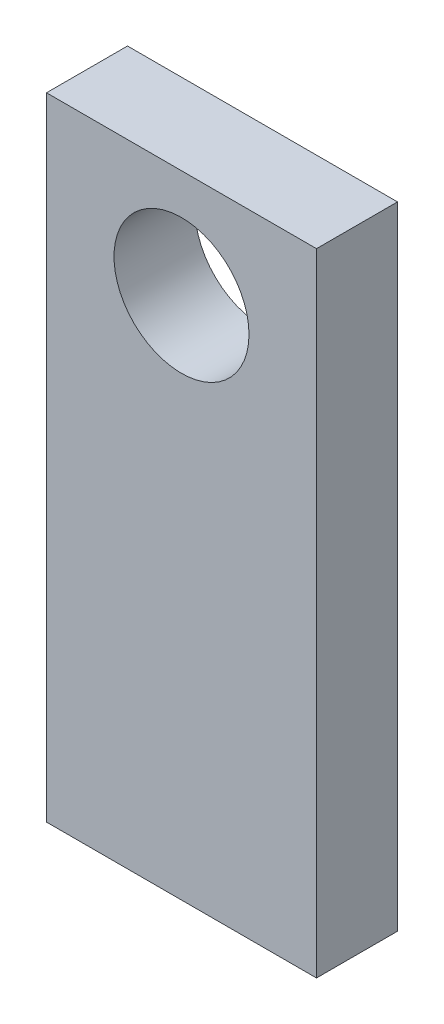
SolidWorks part; units mm, degrees
ref_plane "Alzado" through (0, 0, 0) normal (0, 0, 1) x (1, 0, 0)
ref_plane "Planta" through (0, 0, 0) normal (0, 1, 0) x (1, 0, 0)
ref_plane "Vista lateral" through (0, 0, 0) normal (1, 0, 0) x (0, 0, -1)
sketch "Croquis1" plane through (0, 0, 0) normal (0, 0, 1) x (1, 0, 0)
  line L1 (0, 0) -> (63.5, 0)
  line L2 (0, 0) -> (0, 148.55)
  line L3 (0, 148.55) -> (63.5, 148.55)
  line L4 (63.5, 0) -> (63.5, 148.55)
  dimension "D1" = 148.55
  dimension "D2" = 63.5
extrude "Saliente-Extruir1" add sketch "Croquis1" along normal blind 19.05
sketch "Croquis2" plane through (0, 0, 19.05) normal (0, 0, 1) x (1, 0, 0)
  line L0 (31.75, 148.55) -> (31.75, 123.15) construction
  line L1 (63.5, 148.55) -> (0, 148.55) construction
  circle A0 centre (31.75, 123.15) radius 15.875
  dimension "D2" = 31.75
  dimension "D1" = 25.4
extrude "Cortar-Extruir1" cut sketch "Croquis2" against normal blind 19.05
